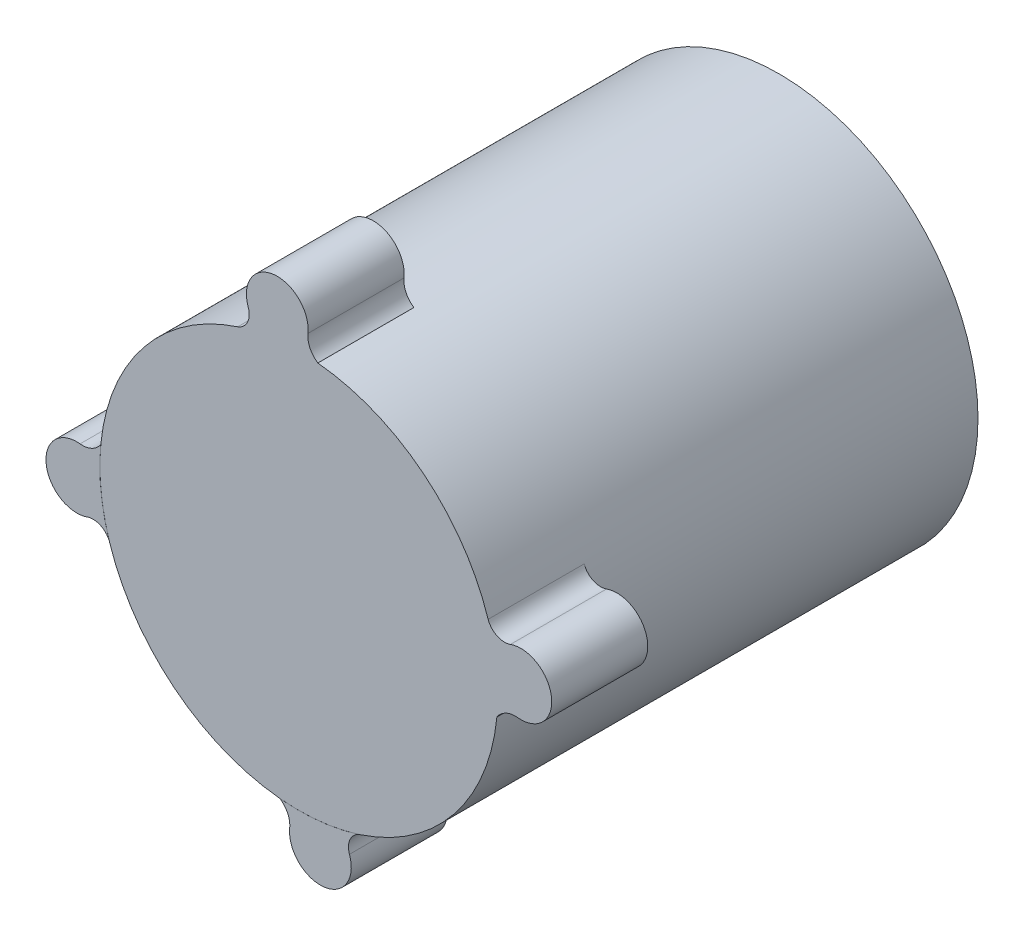
SolidWorks part; units mm, degrees
material "POLIURETAN (11671)"
ref_plane "Płaszczyzna XY" through (0, 0, 0) normal (0, 0, 1) x (1, 0, 0)
ref_plane "Płaszczyzna XZ" through (0, 0, 0) normal (0, 1, 0) x (1, 0, 0)
ref_plane "Płaszczyzna YZ" through (0, 0, 0) normal (1, 0, 0) x (0, 0, -1)
sketch "Szkic1" plane through (0, 0, 0) normal (0, 0, 1) x (1, 0, 0)
  circle A0 centre (0, 0) radius 29
extrude "Dodanie-wyciągnięcie1" add sketch "Szkic1" along normal blind 70
sketch "Szkic2" plane through (0, 0, 70) normal (0, 0, 1) x (1, 0, 0)
  line L0 (2.7554, 28.8771) -> (2.7772, 28.8627)
  line L1 (27.5707, 8.9888) -> (27.5598, 9.0065)
  line L2 (28.8771, -2.7554) -> (28.8585, -2.8211)
  arc A3 (1.3317, 31.8881) -> (-7.3804, 30.8479) centre (-3.1432, 32.3632) ccw
  arc A4 (-7.3804, 30.8479) -> (-8.9888, 27.5707) centre (-9.7771, 29.9908) cw
  arc A5 (31.8881, -1.3317) -> (30.8479, 7.3804) centre (32.3632, 3.1432) ccw
  arc A6 (1.3317, 31.8881) -> (2.7554, 28.8771) centre (4.5132, 31.5504) ccw
  circle A7 centre (-0.0067, -0.0055) radius 29.0021
  arc A8 (31.8881, -1.3317) -> (28.8771, -2.7554) centre (31.5504, -4.5132) ccw
  arc A9 (30.8479, 7.3804) -> (27.5707, 8.9888) centre (29.9908, 9.7771) cw
  arc A10 (-1.3317, -31.8881) -> (7.3804, -30.8479) centre (3.1432, -32.3632) ccw
  arc A11 (-1.3317, -31.8881) -> (-2.7554, -28.8771) centre (-4.5132, -31.5504) ccw
  arc A12 (7.3804, -30.8479) -> (8.8258, -27.63) centre (9.7771, -29.9908) cw
  arc A13 (-31.8881, 1.3317) -> (-30.8479, -7.3804) centre (-32.3632, -3.1432) ccw
  arc A14 (-31.8881, 1.3317) -> (-28.8771, 2.7554) centre (-31.5504, 4.5132) ccw
  arc A15 (-30.8479, -7.3804) -> (-27.6515, -8.7741) centre (-29.9908, -9.7771) cw
  point P34 (0, 0)
  point P41 (0, 0)
  circle M5 centre (0, 0) radius 29
  dimension "D1" = 4
extrude "Dodanie-wyciągnięcie4" add sketch "Szkic2" against normal blind 14 contours A5 A9 L2 A8 M5 | A10 A12 A7 A11 | A13 A15 A7 A14 | A6 A3 A4 L0 M5
